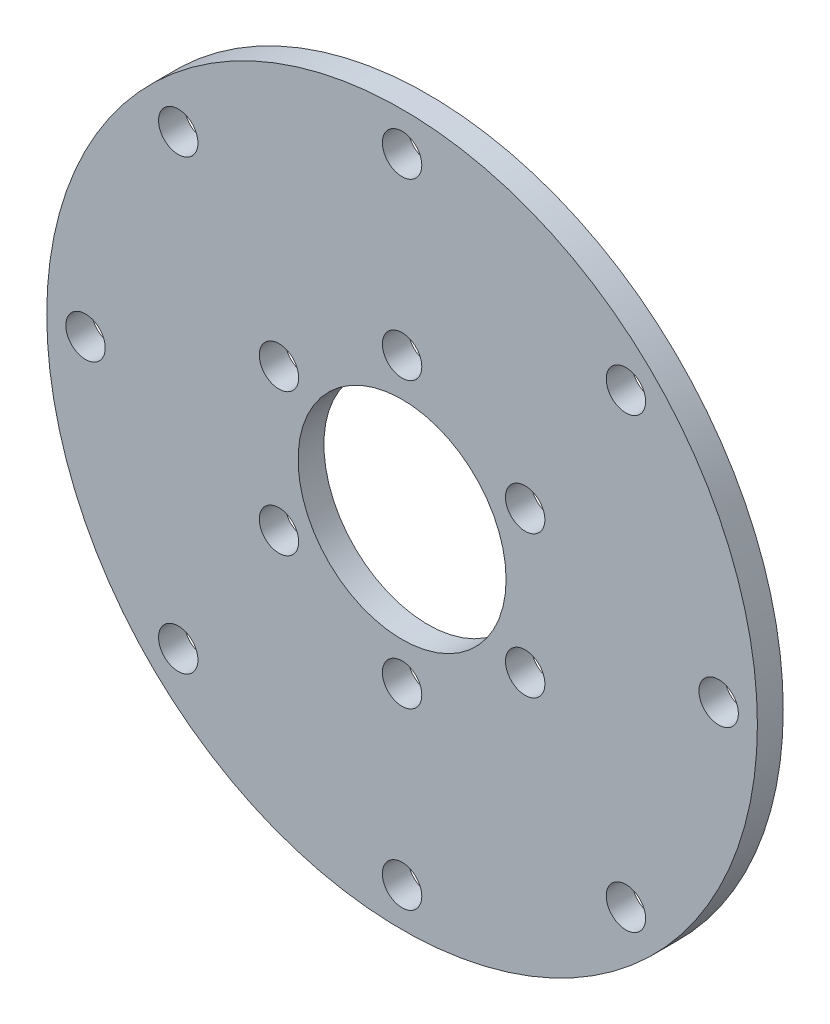
SolidWorks part; units mm, degrees
material "Thornel Mat VMA"
ref_plane "前视基准面" through (0, 0, 0) normal (0, 0, 1) x (1, 0, 0)
ref_plane "上视基准面" through (0, 0, 0) normal (0, 1, 0) x (1, 0, 0)
ref_plane "右视基准面" through (0, 0, 0) normal (1, 0, 0) x (0, 0, -1)
sketch "草图1" plane through (0, 0, 0) normal (0, 0, 1) x (1, 0, 0)
  circle A0 centre (0, 0) radius 8.05
  circle A1 centre (0, 0) radius 21 construction
  circle A2 centre (0, 0) radius 27.5
  dimension "D1" = 16.1
  dimension "D2" = 42
  dimension "D3" = 6.5
extrude "凸台-拉伸1" add sketch "草图1" along normal blind 2
sketch "草图2" plane through (0, 0, 2) normal (0, 0, 1) x (1, 0, 0)
  circle A0 centre (0, 0) radius 11 construction
  circle A1 centre (0, 11) radius 1.525
  circle A2 centre (9.5263, 5.5) radius 1.525
  circle A3 centre (9.5263, -5.5) radius 1.525
  circle A4 centre (0, -11) radius 1.525
  circle A5 centre (-9.5263, -5.5) radius 1.525
  circle A6 centre (-9.5263, 5.5) radius 1.525
  point P29 (0, 0)
  dimension "D1" = 22
  dimension "D2" = 3.05
  dimension "D3" = 6
extrude "切除-拉伸1" cut sketch "草图2" against normal blind 2
sketch "草图3" plane through (0, 0, 2) normal (0, 0, 1) x (1, 0, 0)
  circle A0 centre (0, 0) radius 24.5 construction
  circle A1 centre (0, 0) radius 27.5 construction
  circle A2 centre (0, 24.5) radius 1.525
  circle A3 centre (17.3241, 17.3241) radius 1.525
  circle A4 centre (24.5, 0) radius 1.525
  circle A5 centre (17.3241, -17.3241) radius 1.525
  circle A6 centre (0, -24.5) radius 1.525
  circle A7 centre (-17.3241, -17.3241) radius 1.525
  circle A8 centre (-24.5, 0) radius 1.525
  circle A9 centre (-17.3241, 17.3241) radius 1.525
  point P31 (0, 0)
  dimension "D1" = 3
  dimension "D2" = 3.05
  dimension "D3" = 8
extrude "切除-拉伸2" cut sketch "草图3" against normal blind 2
